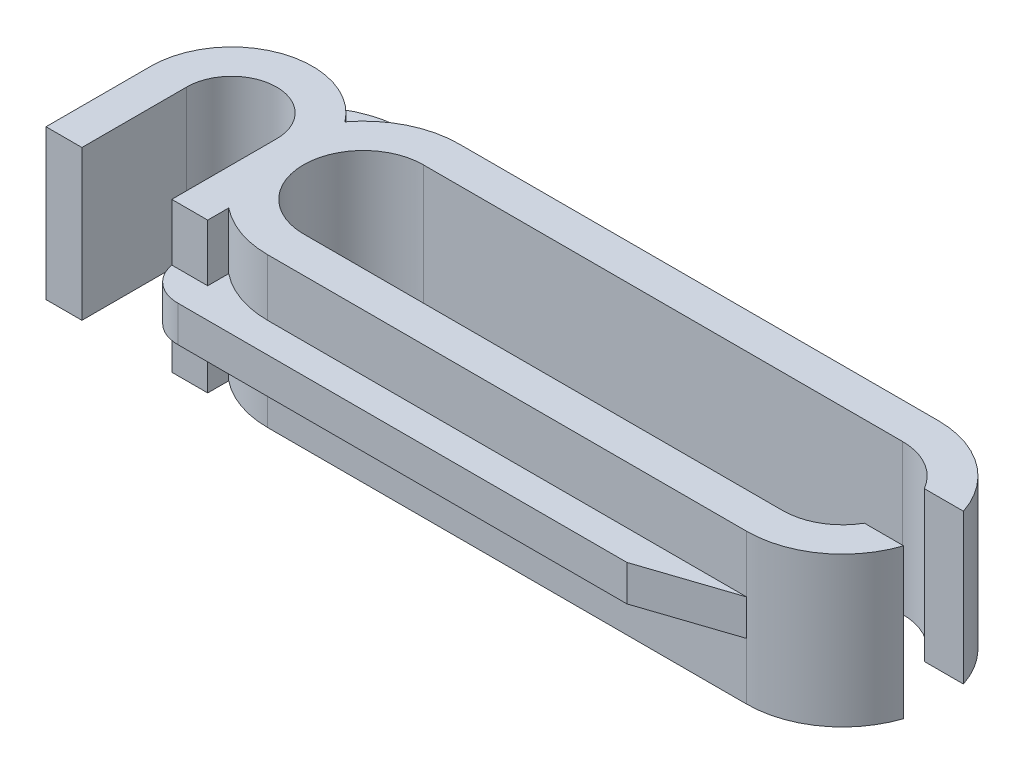
SolidWorks part; units mm, degrees
ref_plane "Front Plane" through (0, 0, 0) normal (0, 0, 1) x (1, 0, 0)
ref_plane "Top Plane" through (0, 0, 0) normal (0, 1, 0) x (1, 0, 0)
ref_plane "Right Plane" through (0, 0, 0) normal (1, 0, 0) x (0, 0, -1)
sketch "Sketch1" plane through (0, 0, 0) normal (0, 1, 0) x (1, 0, 0)
  line L0 (0, -55) -> (0, 55) construction
  line L1 (11.2, -3.2) -> (-11.2, -3.2) construction
  line L2 (11.2, -3.2) -> (11.2, 3.2) construction
  line L3 (11.2, 3.2) -> (-11.2, 3.2) construction
  line L4 (-11.2, -3.2) -> (-11.2, 3.2) construction
  line L5 (11.2, -3.2) -> (-11.2, 3.2) construction
  line L6 (11.2, 3.2) -> (-11.2, -3.2) construction
  line L7 (-11.2, 3.2) -> (-8, 3.2) construction
  line L8 (-11.2, 3.2) -> (-11.2, -3.2) construction
  line L9 (-11.2, -3.2) -> (-8, -3.2) construction
  line L10 (-8, 3.2) -> (-8, -3.2) construction
  line L11 (-11.2, 3.2) -> (-8, -3.2) construction
  line L12 (-11.2, -3.2) -> (-8, 3.2) construction
  line L13 (-8, 3.2) -> (8, 3.2)
  line L14 (8, -3.2) -> (-8, -3.2)
  arc A0 (-8, 3.2) -> (-8, -3.2) centre (-8, 0) ccw
  arc A1 (8, 3.2) -> (8, -3.2) centre (8, 0) cw
  point P0 (0, 0)
  point P8 (-9.6, 0)
  dimension "D1" = 6.4
  dimension "D2" = 22.4
  dimension "D3" = 3.2
extrude "Boss-Extrude1" add sketch "Sketch1" along normal blind 5
sketch "Sketch3" plane through (0, 5, 0) normal (0, 1, 0) x (1, 0, 0)
  line L0 (0, -2.75) -> (0, 2.75) construction
  line L1 (10, -2) -> (-10, -2) construction
  line L2 (10, -2) -> (10, 2) construction
  line L3 (10, 2) -> (-10, 2) construction
  line L4 (-10, -2) -> (-10, 2) construction
  line L5 (10, -2) -> (-10, 2) construction
  line L6 (10, 2) -> (-10, -2) construction
  line L7 (-10, 2) -> (-8, 2) construction
  line L8 (-10, 2) -> (-10, -2) construction
  line L9 (-10, -2) -> (-8, -2) construction
  line L10 (-8, 2) -> (-8, -2) construction
  line L11 (-10, 2) -> (-8, -2) construction
  line L12 (-10, -2) -> (-8, 2) construction
  line L13 (-8, 2) -> (8, 2)
  line L14 (8, -2) -> (-8, -2)
  arc A0 (-8, 2) -> (-8, -2) centre (-8, 0) ccw
  arc A1 (8, 2) -> (8, -2) centre (8, 0) cw
  point P0 (0, 0)
  point P8 (-9, 0)
  dimension "D3" = 2
  dimension "D1" = 4
  dimension "D2" = 20
extrude "Cut-Extrude1" cut sketch "Sketch3" against normal through all
sketch "Sketch4" plane through (0, 5, 0) normal (0, 1, 0) x (1, 0, 0)
  line L1 (-8.5, 1) -> (8.5, 1) construction
  line L2 (-8.5, 1) -> (-8.5, -1) construction
  line L3 (-8.5, -1) -> (8.5, -1) construction
  line L4 (8.5, 1) -> (8.5, -1) construction
  line L5 (-8.5, 1) -> (8.5, -1) construction
  line L6 (-8.5, -1) -> (8.5, 1) construction
  line L7 (8.5, 1) -> (12.5, 1)
  line L8 (8.5, 1) -> (8.5, -1)
  line L9 (8.5, -1) -> (12.5, -1)
  line L10 (12.5, 1) -> (12.5, -1)
  line L11 (8.5, 1) -> (12.5, -1) construction
  line L12 (8.5, -1) -> (12.5, 1) construction
  point P0 (0, 0)
  point P8 (10.5, 0)
  dimension "D1" = 2
  dimension "D2" = 17
  dimension "D3" = 4
extrude "Cut-Extrude2" cut sketch "Sketch4" against normal through all
sketch "Sketch5" plane through (0, 0, 0) normal (0, -1, 0) x (1, 0, 0)
  line L0 (-8, 3.2) -> (-50008, 3.2) construction
  line L1 (-10, -0.3) -> (-10, 3.2)
  line L2 (-10, 3.2) -> (-15.4, 3.2) construction
  line L3 (-10, 3.2) -> (-10, -3) construction
  line L4 (-10, -3) -> (-15.4, -3) construction
  line L5 (-15.4, 3.2) -> (-15.4, -3) construction
  line L6 (-10, 3.2) -> (-15.4, -3) construction
  line L7 (-10, -3) -> (-15.4, 3.2) construction
  line L8 (-15.4, -3) -> (-10, -3) construction
  line L9 (-15.4, -3) -> (-15.4, -0.3) construction
  line L10 (-15.4, -0.3) -> (-10, -0.3) construction
  line L11 (-10, -3) -> (-10, -0.3) construction
  line L12 (-15.4, -3) -> (-10, -0.3) construction
  line L13 (-15.4, -0.3) -> (-10, -3) construction
  line L14 (-10, 3.2) -> (-15.4, 3.2)
  line L15 (-15.4, 3.2) -> (-15.4, -0.3)
  arc A0 (-8, 2) -> (-8, -2) centre (-8, 0) ccw construction
  arc A1 (-15.4, -0.3) -> (-10, -0.3) centre (-12.7, -0.3) ccw
  point P7 (-12.7, 0.1)
  point P13 (-12.7, -1.65)
  dimension "D1" = 6.2
  dimension "D2" = 5.4
  dimension "D3" = 2.7
extrude "Boss-Extrude2" add sketch "Sketch5" against normal blind 5
sketch "Sketch7" plane through (0, 0, 0) normal (0, -1, 0) x (1, 0, 0)
  line L0 (-14.2, -0.3) -> (-14.2, 3.2)
  line L1 (-10, 3.2) -> (-15.4, 3.2) construction
  line L2 (-11.2, -0.3) -> (-11.2, 3.2)
  line L3 (-11.2, 3.2) -> (-14.2, 3.2)
  arc A0 (-11.2, -0.3) -> (-14.2, -0.3) centre (-12.7, -0.3) cw
  dimension "D1" = 1.5
extrude "Cut-Extrude3" cut sketch "Sketch7" against normal through all
ref_plane "Plane1" through (0, 2.5, 0) normal (0, 1, 0) x (1, 0, 0)
sketch "Sketch8" plane through (0, 2.5, 0) normal (0, 1, 0) x (1, 0, 0)
  line L0 (-11.2, 0.3) -> (-11.2, 50000.3) construction
  line L1 (-11.2, 4.6) -> (5, 4.6)
  line L2 (-14.2, 0.3) -> (-14.2, 50000.3) construction
  line L4 (5, 4.6) -> (8, 3.2)
  line L5 (8, 3.2) -> (-8, 3.2)
  arc A1 (-11.2, 4.6) -> (-14.2, 2.545) centre (-11.2, 1.3827) ccw
  arc A2 (-8, 3.2) -> (-10.55, 1.9333) centre (-8, 0) ccw
  arc A3 (-8, 3.2) -> (-10.55, 1.9333) centre (-8, 0) ccw construction
  arc A5 (-10.55, 1.9333) -> (-15.4, 0.3) centre (-12.7, 0.3) ccw construction
  arc A6 (-10.55, 1.9333) -> (-14.2, 2.545) centre (-12.7, 0.3) ccw
  point P2 (-14.2, 2.545)
  dimension "D1" = 1.4
  dimension "D2" = 3
extrude "Boss-Extrude3" add sketch "Sketch8" along normal mid plane 1.2
sketch "Sketch9" plane through (0, 2.5, 0) normal (0, 1, 0) x (1, 0, 0)
  line L0 (-10, -2.498) -> (-10, -3.2) construction
  line L1 (-8, -3.2) -> (8, -3.2)
  line L2 (8, -3.2) -> (5, -4.2)
  line L3 (5, -4.2) -> (-10, -4.2)
  line L4 (-10, -3.2) -> (-10, -50003.2) construction
  line L6 (-11.2, -3.2) -> (-10, -3.2)
  line L7 (-10, -3.2) -> (-10, -2.498)
  arc A0 (-8, -3.2) -> (-10, -2.498) centre (-8, 0) cw
  arc A1 (-10, -4.2) -> (-11.2, -3.2) centre (-10, -2.98) cw
  dimension "D1" = 3
  dimension "D2" = 1
extrude "Boss-Extrude4" add sketch "Sketch9" along normal mid plane 1.2
